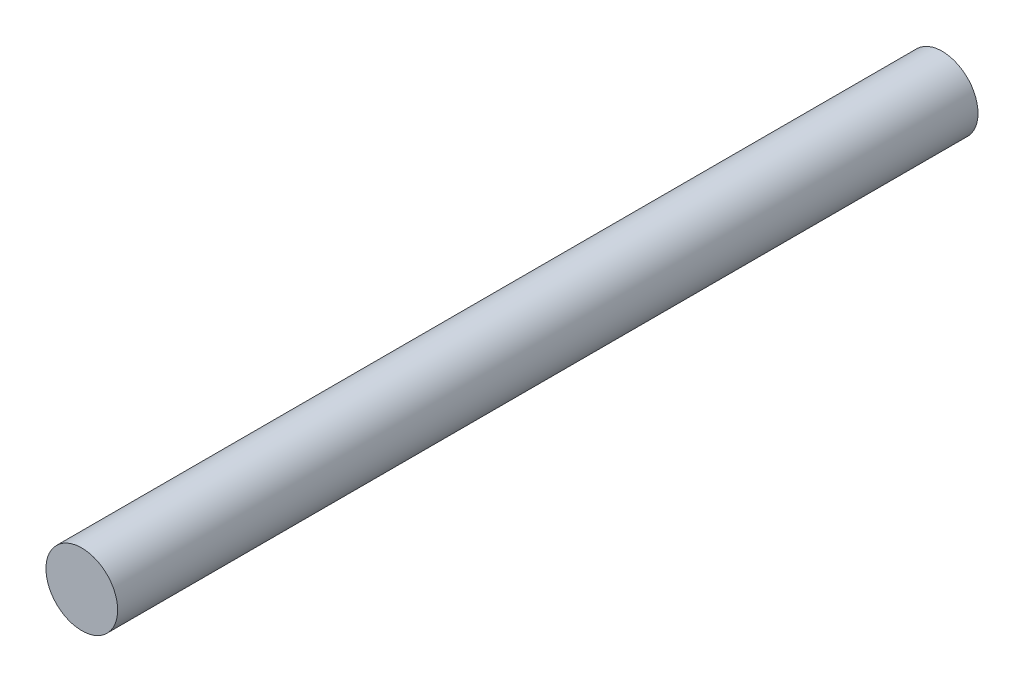
SolidWorks part; units mm, degrees
ref_plane "Ön Düzlem" through (0, 0, 0) normal (0, 0, 1) x (1, 0, 0)
ref_plane "Üst Düzlem" through (0, 0, 0) normal (0, 1, 0) x (1, 0, 0)
ref_plane "Sağ Düzlem" through (0, 0, 0) normal (1, 0, 0) x (0, 0, -1)
sketch "Çizim1" plane through (0, 0, 0) normal (0, 0, 1) x (1, 0, 0)
  circle A0 centre (0, 0) radius 5
  dimension "D1" = 10
extrude "Yükseklik-Ekstrüzyon1" add sketch "Çizim1" along normal blind 120
